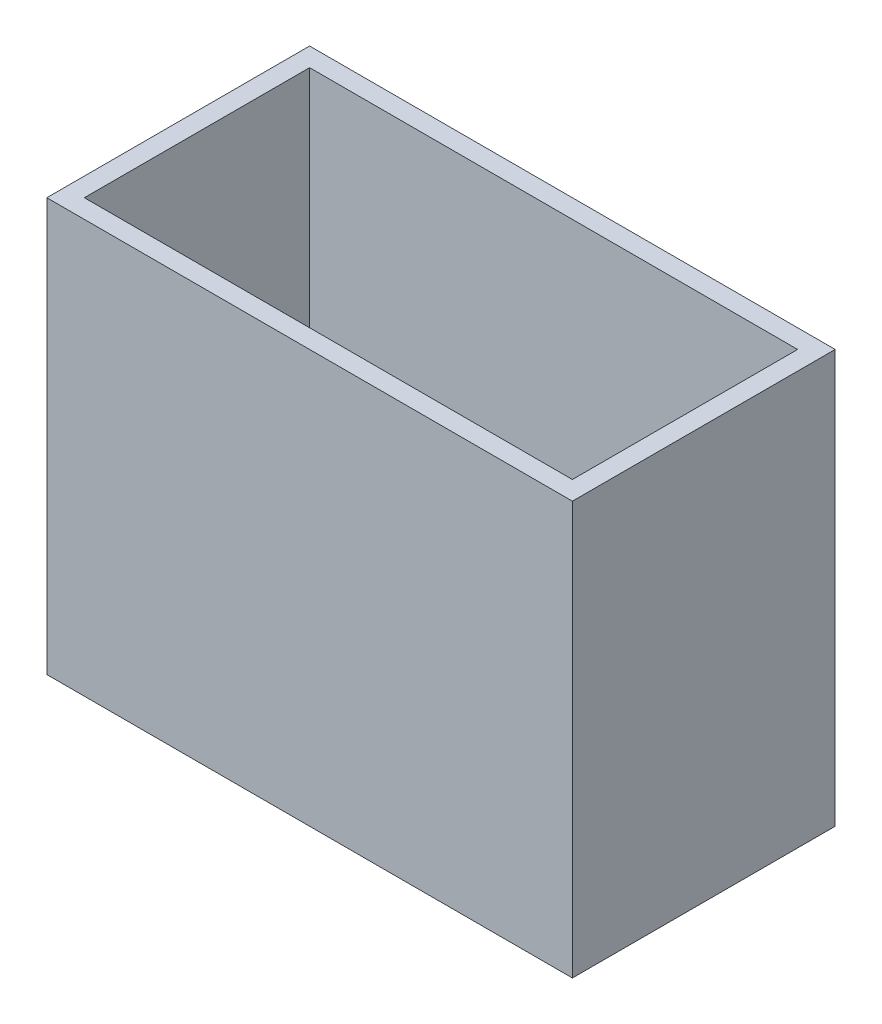
SolidWorks part; units mm, degrees
ref_plane "Plano frontal" through (0, 0, 0) normal (0, 0, 1) x (1, 0, 0)
ref_plane "Plano superior" through (0, 0, 0) normal (0, 1, 0) x (1, 0, 0)
ref_plane "Plano direito" through (0, 0, 0) normal (1, 0, 0) x (0, 0, -1)
sketch "Sketch1" plane through (0, 0, 0) normal (0, 1, 0) x (1, 0, 0)
  line L0 (-6.5, 3) -> (6.5, 3)
  line L1 (-7, 3.5) -> (7, 3.5)
  line L2 (-7, 3.5) -> (-7, -3.5)
  line L3 (-7, -3.5) -> (7, -3.5)
  line L4 (7, 3.5) -> (7, -3.5)
  line L5 (6.5, 3) -> (6.5, -3)
  line L6 (-6.5, -3) -> (6.5, -3)
  line L7 (-6.5, 3) -> (-6.5, -3)
  point P4 (0, 3.5)
  point P6 (-7, 0)
  dimension "D1" = 14
  dimension "D2" = 7
  dimension "D3" = 0.5
extrude "Boss-Extrude1" add sketch "Sketch1" along normal mid plane 11
